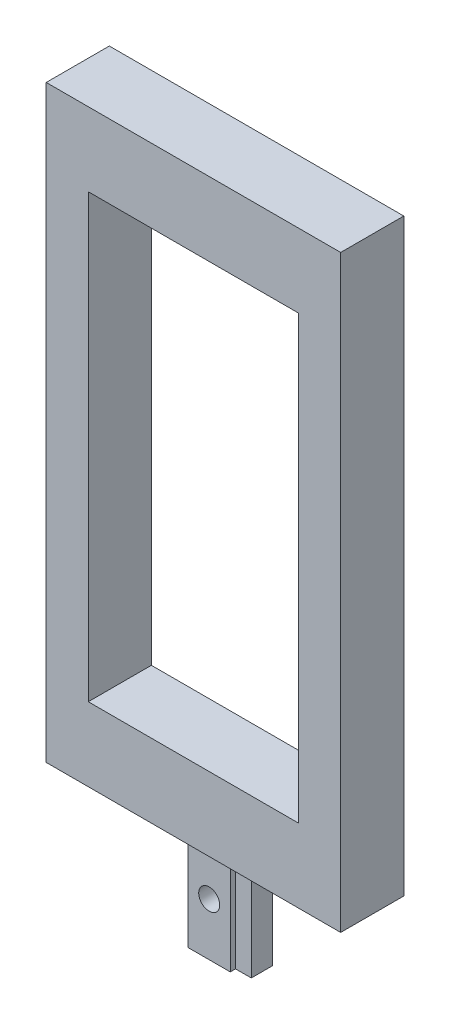
SolidWorks part; units mm, degrees
material "ABS"
ref_plane "Front Plane" through (0, 0, 0) normal (0, 0, 1) x (1, 0, 0)
ref_plane "Top Plane" through (0, 0, 0) normal (0, 1, 0) x (1, 0, 0)
ref_plane "Right Plane" through (0, 0, 0) normal (1, 0, 0) x (0, 0, -1)
sketch "Sketch1" plane through (0, 0, 0) normal (0, 0, 1) x (1, 0, 0)
  line L1 (-10, -21) -> (10, -21)
  line L2 (-10, -21) -> (-10, 21)
  line L3 (-10, 21) -> (10, 21)
  line L4 (10, -21) -> (10, 21)
  line L5 (-10, -21) -> (10, 21) construction
  line L6 (-10, 21) -> (10, -21) construction
  line L7 (-14, -28) -> (14, -28)
  line L8 (-14, -28) -> (-14, 28)
  line L9 (-14, 28) -> (14, 28)
  line L10 (14, -28) -> (14, 28)
  line L11 (-14, -28) -> (14, 28) construction
  line L12 (-14, 28) -> (14, -28) construction
  point P0 (0, 0)
  point P5 (0, 0)
  dimension "D1" = 20
  dimension "D2" = 42
  dimension "D3" = 28
  dimension "D4" = 56
extrude "Boss-Extrude1" add sketch "Sketch1" along normal blind 6
sketch "Sketch2" plane through (0, -28, 0) normal (0, -1, 0) x (1, 0, 0)
  line L0 (0, 6) -> (0, 0) construction
  line L1 (-14, 6) -> (14, 6) construction
  line L3 (-2, 1.5) -> (2, 1.5)
  line L4 (-2, 1.5) -> (-2, 4.5)
  line L5 (-2, 4.5) -> (2, 4.5)
  line L6 (2, 1.5) -> (2, 4.5)
  line L7 (-2, 1.5) -> (2, 4.5) construction
  line L8 (-2, 4.5) -> (2, 1.5) construction
  line L9 (2, 2) -> (3.5, 2)
  line L10 (2, 2) -> (2, 4)
  line L11 (2, 4) -> (3.5, 4)
  line L12 (3.5, 2) -> (3.5, 4)
  line L13 (2, 2) -> (3.5, 4) construction
  line L14 (2, 4) -> (3.5, 2) construction
  point P5 (0, 3)
  point P10 (2.75, 3)
  dimension "D1" = 4
  dimension "D2" = 3
  dimension "D3" = 1.5
  dimension "D4" = 2
  dimension "D5" = 0.75
  dimension "D6" = 1.5
extrude "Boss-Extrude2" add sketch "Sketch2" along normal blind 10 contours L3 L6 L5 L4 | L9 L12 L11 L6
sketch "Sketch3" plane through (0, 0, 4.5) normal (0, 0, 1) x (1, 0, 0)
  line L0 (-2, -38) -> (-2, -28) construction
  line L1 (-2, -38) -> (2, -38) construction
  circle A0 centre (0, -33) radius 1
  dimension "D1" = 2
  dimension "D2" = 2
  dimension "D3" = 5
extrude "Cut-Extrude1" cut sketch "Sketch3" against normal blind 10
